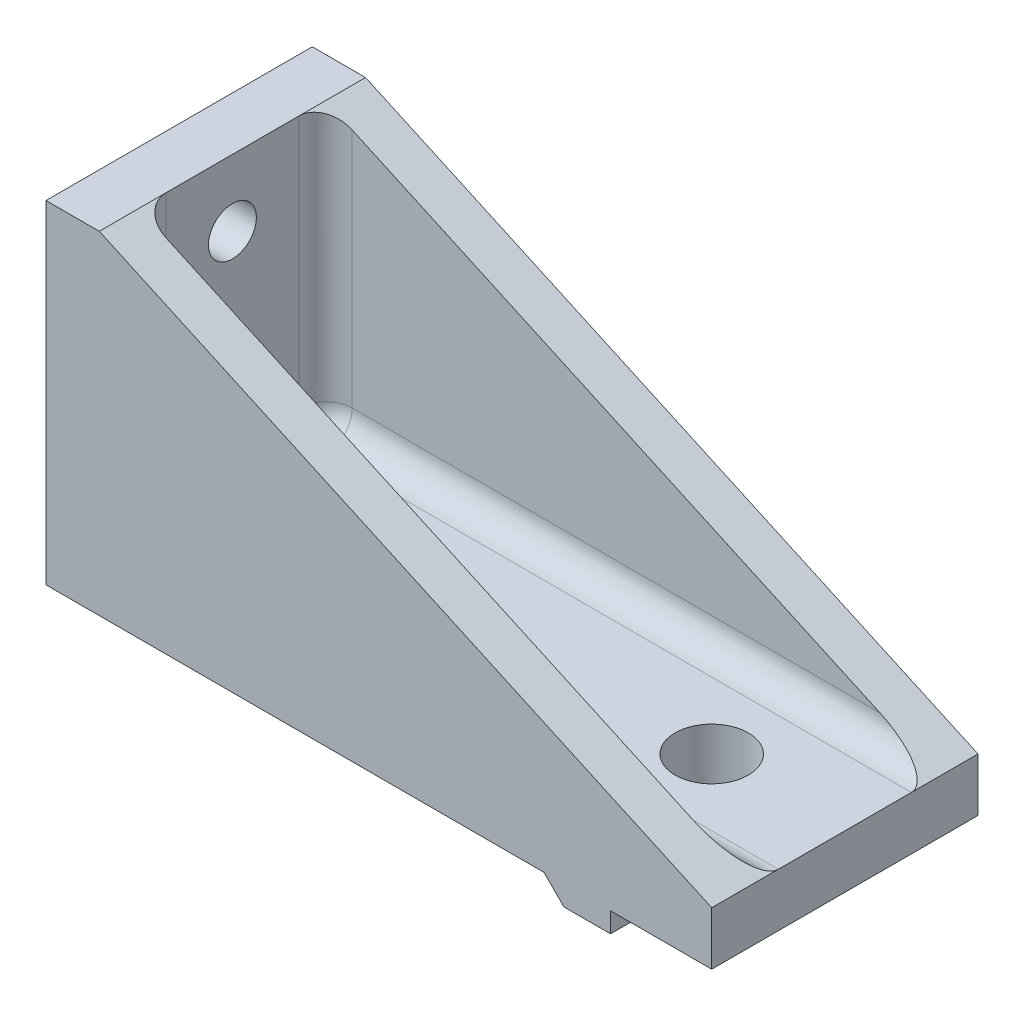
SolidWorks part; units mm, degrees
ref_plane "Alzado" through (0, 0, 0) normal (0, 0, 1) x (1, 0, 0)
ref_plane "Planta" through (0, 0, 0) normal (0, 1, 0) x (1, 0, 0)
ref_plane "Vista lateral" through (0, 0, 0) normal (1, 0, 0) x (0, 0, -1)
sketch "Croquis1" plane through (0, 0, 0) normal (0, 0, 1) x (1, 0, 0)
  line L0 (0, 0) -> (37.4, 0)
  line L1 (50, 0) -> (50, 4)
  line L2 (50, 4) -> (4, 4)
  line L3 (4, 4) -> (4, 25)
  line L4 (4, 25) -> (0, 25)
  line L5 (0, 25) -> (0, 0)
  line L6 (42.4, 0) -> (50, 0)
  line L8 (55, 0) -> (-55, 0) construction
  line L9 (42.4, 0) -> (42.4, -1.5)
  line L10 (42.4, -1.5) -> (38.9, -1.5)
  line L11 (37.4, 0) -> (38.9, -1.5)
  dimension "D1" = 25
  dimension "D2" = 4
  dimension "D3" = 4
  dimension "D4" = 50
  dimension "D5" = 3.5
  dimension "D6" = 1.5
  dimension "D7" = 45
  dimension "D8" = 7.6
extrude "Saliente-Extruir1" add sketch "Croquis1" along normal mid plane 20
sketch "Croquis7" plane through (50, 0, 0) normal (1, 0, 0) x (0, 0, -1)
  line L0 (-10, 0) -> (10, 0) construction
  line L1 (-3, 0) -> (3, 0)
  line L2 (-3, 0) -> (-3, -1.5)
  line L3 (-3, -1.5) -> (3, -1.5)
  line L4 (3, 0) -> (3, -1.5)
  line L5 (-10, -1.5) -> (10, -1.5) construction
  line L6 (0, -6.5262) -> (0, 7.9576) construction
  dimension "D1" = 6
extrude "Cortar-Extruir3" cut sketch "Croquis7" against normal through all
sketch "Croquis3" plane through (0, 0, 0) normal (0, -1, 0) x (1, 0, 0)
  line L0 (40, 20) -> (40, 0) construction
  line L3 (0, 0) -> (50, 0) construction
  line L4 (0, 10) -> (0, -10) construction
  line L5 (50, 10) -> (50, -10) construction
  circle A0 centre (40, 0) radius 2.75
  dimension "D1" = 5.5
  dimension "D2" = 10
extrude "Cortar-Extruir1" cut sketch "Croquis3" against normal blind 20
sketch "Croquis4" plane through (4, 0, 0) normal (1, 0, 0) x (0, 0, -1)
  line L0 (-10, 25) -> (10, 25) construction
  line L2 (0, 16.4545) -> (0, 6.7142) construction
  circle A0 centre (0, 20) radius 1.8
  circle A1 centre (0, 10) radius 1.8
  dimension "D2" = 3.6
  dimension "D1" = 5
  dimension "D3" = 10
extrude "Cortar-Extruir2" cut sketch "Croquis4" against normal blind 20
sketch "Croquis5" plane through (0, 0, -10) normal (0, 0, -1) x (-1, 0, 0)
  line L2 (0, 25) -> (0, 0) construction
  line L3 (0, 0) -> (-50, 0)
  line L4 (-50, 0) -> (-50, 4) construction
  line L5 (-4, 25) -> (0, 25) construction
  line L6 (-50, 0) -> (-50, 4)
  line L7 (-4, 25) -> (0, 25)
  line L8 (-4, 25) -> (-50, 4)
  line L9 (0, 25) -> (0, 0)
extrude "Saliente-Extruir2" add sketch "Croquis5" against normal blind 3
mirror "Simetría1" about plane through (0, 0, 0) normal (0, 0, 1) of "Saliente-Extruir2"
fillet "Redondeo1" radius 2 5 edges at (4, 4, 0) (4, 14.5, -7) (4, 14.5, 7) (27, 4, 7) (27, 4, -7)
